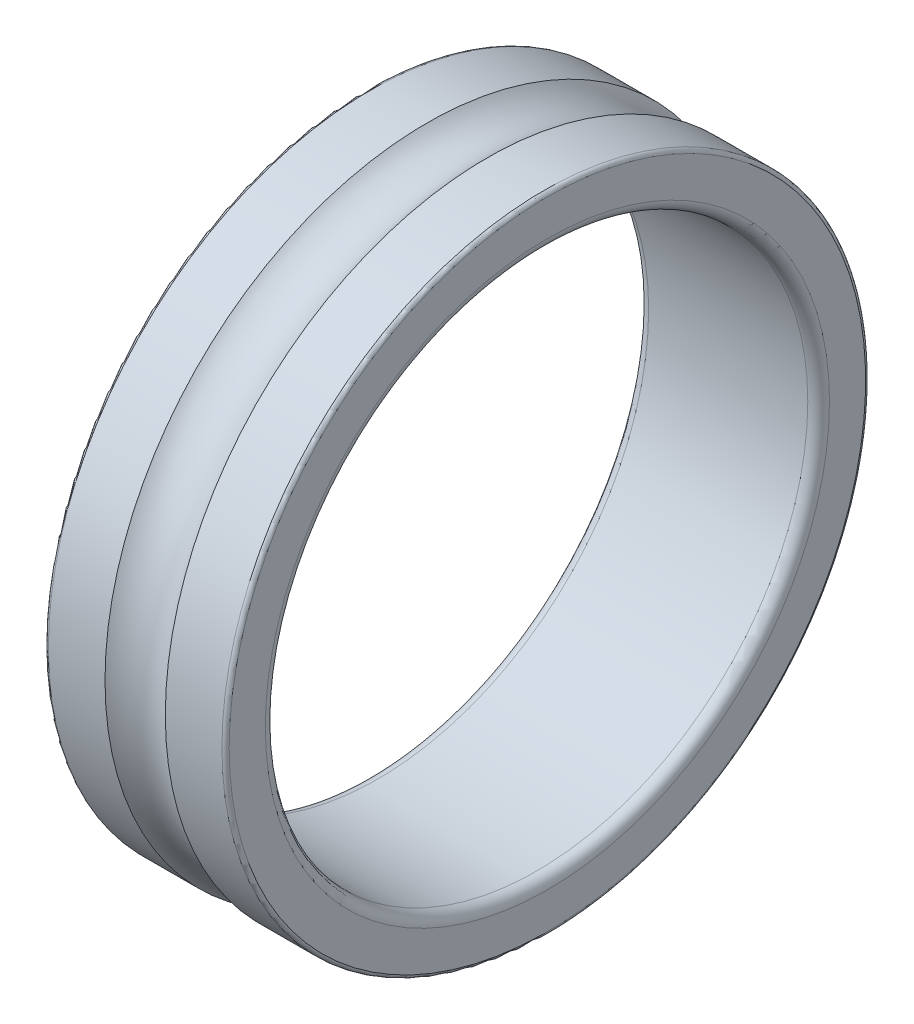
SolidWorks part; units mm, degrees
material "普通碳钢"
ref_plane "前视基准面" through (0, 0, 0) normal (0, 0, 1) x (1, 0, 0)
ref_plane "上视基准面" through (0, 0, 0) normal (0, 1, 0) x (1, 0, 0)
ref_plane "右视基准面" through (0, 0, 0) normal (1, 0, 0) x (0, 0, -1)
ref_plane "基准面1" through (0, 0, 0) normal (0, 0, 1) x (1, 0, 0)
sketch "草图1" plane through (0, 0, 0) normal (0, 0, 1) x (1, 0, 0)
  line L0 (0, 8.8) -> (0, 7.8)
  line L1 (0.3, 7.5) -> (4.7, 7.5)
  line L2 (5, 7.8) -> (5, 8.8)
  line L3 (4.9, 8.9) -> (3.3335, 8.9)
  line L4 (1.6665, 8.9) -> (0.1, 8.9)
  line L5 (50, 0) -> (-50, 0) construction
  arc A0 (0, 7.8) -> (0.3, 7.5) centre (0.3, 7.8) ccw
  arc A1 (4.7, 7.5) -> (5, 7.8) centre (4.7, 7.8) ccw
  arc A2 (5, 8.8) -> (4.9, 8.9) centre (4.9, 8.8) ccw
  arc A3 (3.3335, 8.9) -> (1.6665, 8.9) centre (2.5, 9.75) cw
  arc A4 (0.1, 8.9) -> (0, 8.8) centre (0.1, 8.8) ccw
revolve "旋转1" add sketch "草图1" angle 360 about L5
